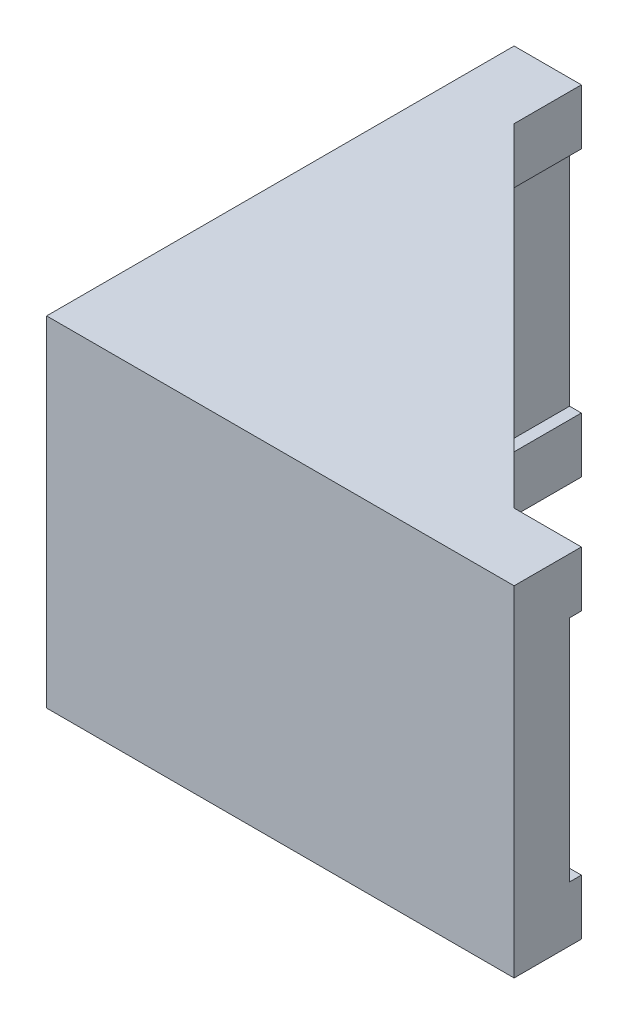
SolidWorks part; units mm, degrees
material "1060 Alloy"
ref_plane "Front Plane" through (0, 0, 0) normal (0, 0, 1) x (1, 0, 0)
ref_plane "Top Plane" through (0, 0, 0) normal (0, 1, 0) x (1, 0, 0)
ref_plane "Right Plane" through (0, 0, 0) normal (1, 0, 0) x (0, 0, -1)
sketch "Sketch1" plane through (0, 0, 0) normal (0, 1, 0) x (1, 0, 0)
  line L0 (0, 0) -> (27.8, 0)
  line L1 (27.8, 0) -> (27.8, 4)
  line L3 (4, 27.8) -> (0, 27.8)
  line L4 (0, 27.8) -> (0, 0)
  line L5 (4, 27.8) -> (4, 23.8)
  line L6 (4, 23.8) -> (23.8, 4)
  line L7 (23.8, 4) -> (27.8, 4)
  dimension "D1" = 27.8
  dimension "D2" = 27.8
  dimension "D3" = 4
  dimension "D4" = 4
  dimension "D5" = 4
  dimension "D6" = 4
extrude "Boss-Extrude1" add sketch "Sketch1" along normal blind 3.3
sketch "Sketch2" plane through (0, 0, 0) normal (0, -1, 0) x (1, 0, 0)
  line L0 (0, 0) -> (27.8, 0)
  line L4 (3.3, -3.3) -> (3.3, -27.8)
  line L5 (4, -27.8) -> (0, -27.8) construction
  line L6 (3.3, -27.8) -> (0, -27.8)
  line L7 (0, -27.8) -> (0, 0)
  line L8 (3.3, -3.3) -> (27.8, -3.3)
  line L9 (27.8, 0) -> (27.8, -4) construction
  line L10 (27.8, -3.3) -> (27.8, 0)
  dimension "D1" = 3.3
  dimension "D2" = 3.3
  dimension "D3" = 3.3
extrude "Boss-Extrude2" add sketch "Sketch2" along normal blind 13.6
sketch "Sketch3" plane through (0, -13.6, 0) normal (0, -1, 0) x (1, 0, 0)
  line L0 (27.8, -3.3) -> (27.8, 0) construction
  line L1 (27.8, -3.3) -> (27.8, -4) construction
  line L2 (0, -27.8) -> (3.3, -27.8) construction
  line L3 (4, -27.8) -> (3.3, -27.8) construction
  line L4 (4, -23.8) -> (4, -27.8) construction
  line L5 (0, 0) -> (0, -27.8) construction
  line L6 (27.8, 0) -> (0, 0) construction
  line L7 (27.8, -4) -> (23.8, -4) construction
  line L8 (23.8, -4) -> (4, -23.8) construction
  line L9 (27.8, -3.3) -> (27.8, 0)
  line L10 (27.8, -3.3) -> (27.8, -4)
  line L11 (0, -27.8) -> (3.3, -27.8)
  line L12 (4, -27.8) -> (3.3, -27.8)
  line L13 (4, -23.8) -> (4, -27.8)
  line L14 (0, 0) -> (0, -27.8)
  line L15 (27.8, 0) -> (0, 0)
  line L16 (27.8, -4) -> (23.8, -4)
  line L17 (23.8, -4) -> (4, -23.8)
extrude "Boss-Extrude3" add sketch "Sketch3" along normal blind 3.3
